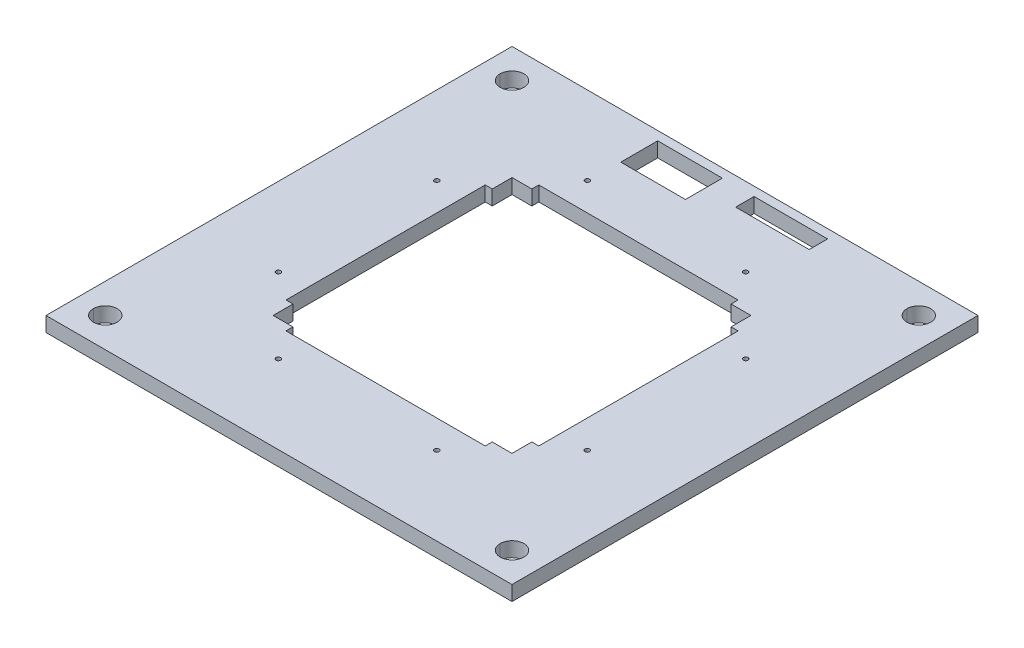
SolidWorks part; units mm, degrees
ref_plane "Front Plane" through (0, 0, 0) normal (0, 0, 1) x (1, 0, 0)
ref_plane "Top Plane" through (0, 0, 0) normal (0, 1, 0) x (1, 0, 0)
ref_plane "Right Plane" through (0, 0, 0) normal (1, 0, 0) x (0, 0, -1)
sketch "Sketch1" plane through (0, 0, 0) normal (0, 1, 0) x (1, 0, 0)
  line L0 (-100.0125, 99.9889) -> (-87.3125, 99.9889) construction
  line L1 (-100.0125, -100.0361) -> (100.0125, -100.0361)
  line L2 (-100.0125, -100.0361) -> (-100.0125, 99.9889)
  line L3 (-100.0125, 99.9889) -> (100.0125, 99.9889)
  line L4 (100.0125, -100.0361) -> (100.0125, 99.9889)
  line L5 (-100.0125, -100.0361) -> (100.0125, 99.9889) construction
  line L6 (-100.0125, 99.9889) -> (100.0125, -100.0361) construction
  line L7 (-74.6125, -74.6125) -> (74.6125, -74.6125) construction
  line L8 (-74.6125, -74.6125) -> (-74.6125, 74.6125) construction
  line L9 (-74.6125, 74.6125) -> (74.6125, 74.6125) construction
  line L10 (74.6125, -74.6125) -> (74.6125, 74.6125) construction
  line L11 (-74.6125, -74.6125) -> (74.6125, 74.6125) construction
  line L12 (-74.6125, 74.6125) -> (74.6125, -74.6125) construction
  line L13 (-87.3125, 99.9889) -> (-87.3125, -100.0361) construction
  line L14 (0, -55) -> (0, 55) construction
  line L15 (-55, 0) -> (55, 0) construction
  line L16 (-100.0125, 96.1789) -> (100.0125, 96.1789) construction
  line L17 (38.5, 54.27) -> (42.77, 54.27)
  line L18 (-33.6459, 96.1789) -> (-5.887, 96.1789)
  line L19 (-33.6459, 96.1789) -> (-33.6459, 80.3284)
  line L20 (-33.6459, 80.3284) -> (-5.887, 80.3284)
  line L21 (-5.887, 96.1789) -> (-5.887, 80.3284)
  line L22 (7.7239, 96.1789) -> (39.2871, 96.1789)
  line L23 (7.7239, 96.1789) -> (7.7239, 88.2654)
  line L24 (7.7239, 88.2654) -> (39.2871, 88.2654)
  line L25 (39.2871, 96.1789) -> (39.2871, 88.2654)
  line L26 (42.77, 54.27) -> (42.77, 51.27)
  line L27 (49, 51.27) -> (42.77, 51.27)
  line L28 (49, 51.27) -> (51.27, 51.27)
  line L29 (51.27, 51.27) -> (51.27, 49)
  line L30 (51.27, 42.77) -> (51.27, 49)
  line L31 (54.27, 42.77) -> (51.27, 42.77)
  line L32 (54.27, 42.77) -> (54.27, 38.5)
  line L33 (54.27, -38.5) -> (54.27, 38.5)
  line L47 (54.27, -38.5) -> (54.27, -42.77)
  line L48 (54.27, -42.77) -> (51.27, -42.77)
  line L49 (51.27, -49) -> (51.27, -42.77)
  line L50 (51.27, -51.2936) -> (51.27, -49)
  line L51 (48.9988, -51.2936) -> (51.27, -51.2936)
  line L52 (42.77, -51.271) -> (48.9988, -51.2936)
  line L53 (42.77, -54.27) -> (42.77, -51.271)
  line L54 (42.77, -54.27) -> (38.5, -54.27)
  line L56 (38.5, -54.27) -> (-38.5, -54.27)
  line L57 (-42.77, -54.27) -> (-38.5, -54.27)
  line L58 (-42.77, -54.27) -> (-42.77, -51.271)
  line L60 (-42.77, -51.271) -> (-48.9988, -51.2936)
  line L61 (-48.9988, -51.2936) -> (-51.27, -51.2936)
  line L62 (-51.27, -51.2936) -> (-51.27, -49)
  line L63 (-51.27, -49) -> (-51.27, -42.77)
  line L65 (-54.27, -42.77) -> (-51.27, -42.77)
  line L66 (-54.27, -38.5) -> (-54.27, -42.77)
  line L67 (-54.27, -38.5) -> (-54.27, 38.5)
  line L68 (-54.27, 42.77) -> (-54.27, 38.5)
  line L70 (49, -49) -> (-49, 49) construction
  line L71 (49, 49) -> (-49, -49) construction
  line L76 (0, 53) -> (0, -53) construction
  line L77 (-54.27, 42.77) -> (-51.27, 42.77)
  line L79 (-51.27, 42.77) -> (-51.27, 49)
  line L80 (-51.27, 51.27) -> (-51.27, 49)
  line L81 (-49, 51.27) -> (-51.27, 51.27)
  line L82 (-49, 51.27) -> (-42.77, 51.27)
  line L84 (-42.77, 54.27) -> (-42.77, 51.27)
  line L85 (-38.5, 54.27) -> (-42.77, 54.27)
  line L86 (-38.5, 54.27) -> (38.5, 54.27)
  circle A0 centre (-87.3125, 87.2889) radius 5.08
  circle A1 centre (87.3125, 87.2889) radius 5.08
  circle A2 centre (-87.3125, -87.2889) radius 5.08
  circle A3 centre (87.3125, -87.2889) radius 5.08
  point P6 (0, 54.27)
  point P11 (-87.3125, 87.2889)
  point P60 (0, -54.27)
  dimension "D5" = 10.16
  dimension "D7" = 85.54
  dimension "D8" = 2.999
  dimension "D1" = 200.025
  dimension "D2" = 200.025
  dimension "D3" = 149.225
  dimension "D4" = 12.7
  dimension "D6" = 3.81
  dimension "D9" = 8.5
  dimension "D10" = 8.5236
  dimension "D11" = 3
extrude "Boss-Extrude1" add sketch "Sketch1" along normal blind 6.35
sketch "Sketch2" plane through (0, 6.35, 0) normal (0, 1, 0) x (1, 0, 0)
  line L0 (-100.0125, -100.0125) -> (100.0125, -100.0125)
  line L1 (-100.0125, -100.0125) -> (-100.0125, 100.0125)
  line L2 (-100.0125, 100.0125) -> (100.0125, 100.0125)
  line L3 (100.0125, -100.0125) -> (100.0125, 100.0125)
  line L4 (-74.6125, -74.6125) -> (74.6125, -74.6125)
  line L5 (-74.6125, -74.6125) -> (-74.6125, 74.6125)
  line L6 (-74.6125, 74.6125) -> (74.6125, 74.6125)
  line L7 (74.6125, -74.6125) -> (74.6125, 74.6125)
  line L8 (-33.6459, 96.2025) -> (-5.887, 96.2025)
  line L9 (-33.6459, 96.2025) -> (-33.6459, 80.3284)
  line L10 (-33.6459, 80.3284) -> (-5.887, 80.3284)
  line L11 (-5.887, 96.2025) -> (-5.887, 80.3284)
  line L12 (7.7239, 96.2025) -> (39.2871, 96.2025)
  line L13 (7.7239, 96.2025) -> (7.7239, 88.2654)
  line L14 (7.7239, 88.2654) -> (39.2871, 88.2654)
  line L15 (39.2871, 96.2025) -> (39.2871, 88.2654)
  circle A0 centre (-87.3125, 87.3125) radius 5.08
  circle A1 centre (87.3125, 87.3125) radius 5.08
  circle A2 centre (-87.3125, -87.3125) radius 5.08
  circle A3 centre (87.3125, -87.3125) radius 5.08
extrude "Boss-Extrude2" add sketch "Sketch2" against normal blind 6.3503
sketch "Sketch3" plane through (0, 0, 0) normal (0, -1, 0) x (1, 0, 0)
  line L0 (-74.6125, -66.3125) -> (74.6125, -66.3125) construction
  line L1 (-74.6125, 74.6125) -> (-74.6125, -74.6125) construction
  line L2 (74.6125, -74.6125) -> (74.6125, 74.6125) construction
  line L3 (74.6125, -74.6125) -> (-74.6125, -74.6125) construction
  line L4 (0, -66.3125) -> (0, -54.27) construction
  line L5 (42.77, -54.27) -> (-42.77, -54.27) construction
  circle A0 centre (-33.9999, -66.3125) radius 1
  circle A1 centre (33.9999, -66.3125) radius 1
  circle A2 centre (-66.3125, 33.9999) radius 1
  circle A3 centre (-66.3125, -33.9999) radius 1
  circle A4 centre (33.9999, 66.3125) radius 1
  circle A5 centre (-33.9999, 66.3125) radius 1
  circle A6 centre (66.3125, -33.9999) radius 1
  circle A7 centre (66.3125, 33.9999) radius 1
  point P19 (0, 0)
  dimension "D2" = 4
  dimension "D1" = 8.3
  dimension "D3" = 33.9999
extrude "Cut-Extrude1" cut sketch "Sketch3" against normal blind 23.622
